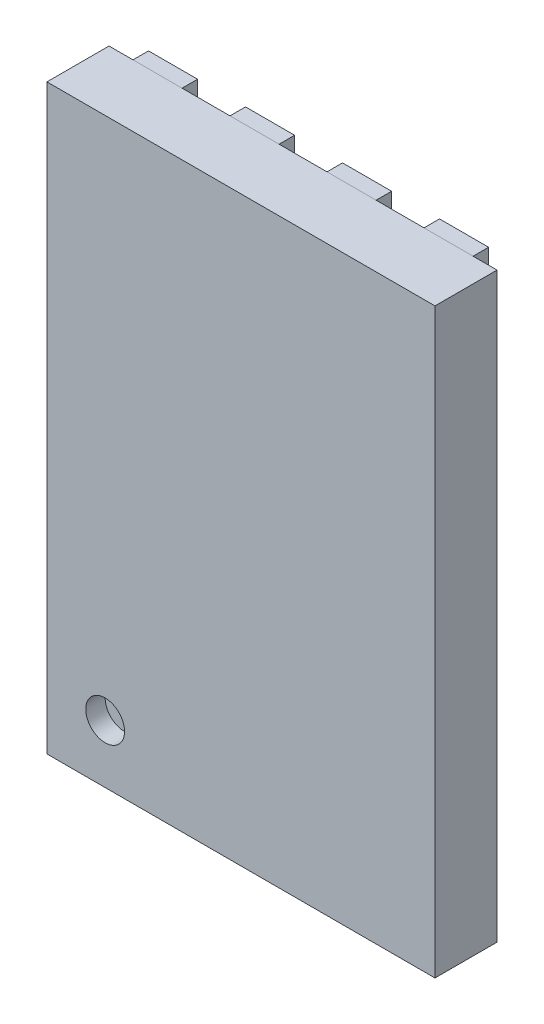
SolidWorks part; units mm, degrees
ref_plane "Front Plane" through (0, 0, 0) normal (0, 0, 1) x (1, 0, 0)
ref_plane "Top Plane" through (0, 0, 0) normal (0, 1, 0) x (1, 0, 0)
ref_plane "Right Plane" through (0, 0, 0) normal (1, 0, 0) x (0, 0, -1)
sketch "Sketch1" plane through (0, 0, 0) normal (0, 0, 1) x (1, 0, 0)
  line L1 (0, 0) -> (2, 0)
  line L2 (0, 0) -> (0, 3)
  line L3 (0, 3) -> (2, 3)
  line L4 (2, 0) -> (2, 3)
  dimension "D1" = 2
  dimension "D2" = 3
extrude "Boss-Extrude1" add sketch "Sketch1" along normal blind 0.32
sketch "Sketch2" plane through (0, 0, 0.32) normal (0, 0, 1) x (1, 0, 0)
  line L0 (0, 3) -> (0, 0) construction
  line L1 (0, 0) -> (2, 0) construction
  circle A0 centre (0.3, 0.3) radius 0.1
  dimension "D3" = 0.2
  dimension "D1" = 0.3
  dimension "D2" = 0.3
extrude "Cut-Extrude1" cut sketch "Sketch2" against normal blind 0.1
sketch "Sketch3" plane through (0, 0, 0) normal (0, 0, -1) x (-1, 0, 0)
  line L0 (-1, 3) -> (-1, 0) construction
  line L1 (-2, 3) -> (0, 3) construction
  line L2 (0, 0) -> (-2, 0) construction
  line L3 (-0.5386, 0.625) -> (-0.185, 0.9786)
  line L4 (-2, 0) -> (-2, 3) construction
  line L5 (-2, 1.5) -> (0, 1.5) construction
  line L6 (0, 3) -> (0, 0) construction
  line L7 (-1.815, 2.375) -> (-0.185, 2.375)
  line L8 (-1.815, 2.375) -> (-1.815, 0.625)
  line L9 (-1.815, 0.625) -> (-0.5386, 0.625)
  line L10 (-0.185, 2.375) -> (-0.185, 0.9786)
  line L11 (-1.75, 3) -> (-1.75, 2.6) construction
  line L12 (-1.8765, 3) -> (-1.6235, 3)
  line L13 (-1.8765, 3) -> (-1.8765, 2.6)
  line L14 (-1.8765, 2.6) -> (-1.6235, 2.6)
  line L15 (-1.6235, 3) -> (-1.6235, 2.6)
  line L16 (-1.3765, 3) -> (-1.1235, 3)
  line L17 (-1.3765, 3) -> (-1.3765, 2.6)
  line L18 (-1.3765, 2.6) -> (-1.1235, 2.6)
  line L19 (-1.1235, 3) -> (-1.1235, 2.6)
  line L20 (-0.8765, 3) -> (-0.6235, 3)
  line L21 (-0.8765, 3) -> (-0.8765, 2.6)
  line L22 (-0.8765, 2.6) -> (-0.6235, 2.6)
  line L23 (-0.6235, 3) -> (-0.6235, 2.6)
  line L24 (-0.3765, 3) -> (-0.1235, 3)
  line L25 (-0.3765, 3) -> (-0.3765, 2.6)
  line L26 (-0.3765, 2.6) -> (-0.1235, 2.6)
  line L27 (-0.1235, 3) -> (-0.1235, 2.6)
  line L28 (-1.3765, 0.4) -> (-1.1235, 0.4)
  line L29 (-1.3765, 0.4) -> (-1.3765, 0)
  line L30 (-1.3765, 0) -> (-1.1235, 0)
  line L31 (-1.1235, 0.4) -> (-1.1235, 0)
  line L32 (-0.8765, 0.4) -> (-0.6235, 0.4)
  line L33 (-0.8765, 0.4) -> (-0.8765, 0)
  line L34 (-0.8765, 0) -> (-0.6235, 0)
  line L35 (-0.6235, 0.4) -> (-0.6235, 0)
  line L36 (-0.3765, 0.4) -> (-0.1235, 0.4)
  line L37 (-0.3765, 0.4) -> (-0.3765, 0)
  line L38 (-0.3765, 0) -> (-0.1235, 0)
  line L39 (-0.1235, 0.4) -> (-0.1235, 0)
  line L40 (-1.8765, 0.4) -> (-1.6235, 0.4)
  line L41 (-1.8765, 0.4) -> (-1.8765, 0)
  line L42 (-1.8765, 0) -> (-1.6235, 0)
  line L43 (-1.6235, 0.4) -> (-1.6235, 0)
  point P16 (-1, 2.375)
  point P19 (-1.815, 1.5)
  dimension "D1" = 1.75
  dimension "D2" = 1.63
  dimension "D3" = 45
  dimension "D4" = 0.5
  dimension "D5" = 0.4
  dimension "D6" = 0.253
  dimension "D7" = 0.75
  dimension "D8" = 4
  dimension "D9" = 2
extrude "Boss-Extrude2" add sketch "Sketch3" along normal blind 0.08 separate body
